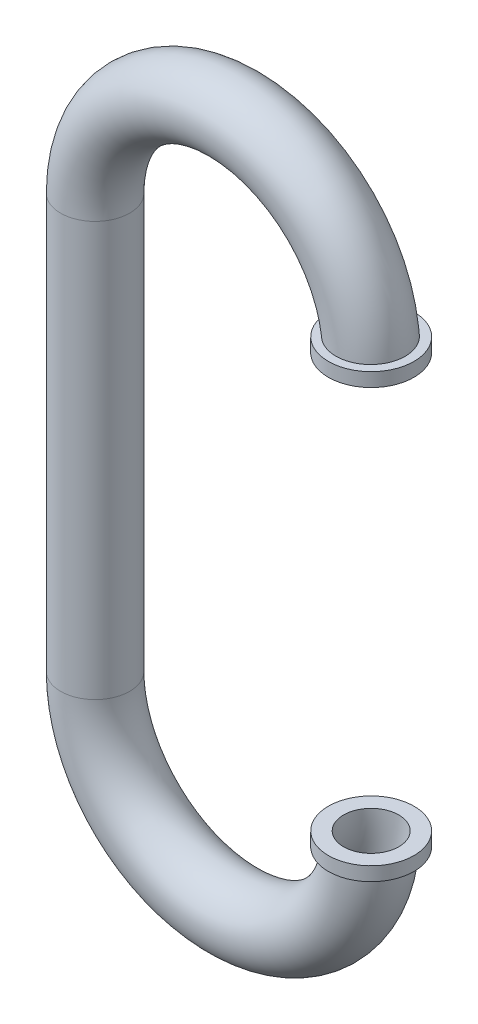
SolidWorks part; units mm, degrees
ref_plane "Ön Düzlem" through (0, 0, 0) normal (0, 0, 1) x (1, 0, 0)
ref_plane "Üst Düzlem" through (0, 0, 0) normal (0, 1, 0) x (1, 0, 0)
ref_plane "Sağ Düzlem" through (0, 0, 0) normal (1, 0, 0) x (0, 0, -1)
sketch "Çizim1" plane through (0, 0, 0) normal (0, 0, 1) x (1, 0, 0)
  line L0 (-2, 0) -> (-2, -3)
  arc A0 (0, 0) -> (-1, 1) centre (-1, 0) ccw
  arc A1 (-1, 1) -> (-2, 0) centre (-1, 0) ccw
  arc A2 (-2, -3) -> (-1, -4) centre (-1, -3) ccw
  arc A3 (-1, -4) -> (0, -3) centre (-1, -3) ccw
sketch "Çizim2" plane through (0, 0, 0) normal (0, 0, 1) x (1, 0, 0)
  line L0 (0, 0) -> (0, 0.1)
sketch "Çizim3" plane through (0, 0, 0) normal (0, 0, 1) x (1, 0, 0)
  line L0 (0, -3) -> (0, -3.1)
ref_plane "Düzlem1" through (0, -3, 0) normal (0, 1, 0) x (1, 0, 0)
sketch "Çizim4" plane through (0, 0, 0) normal (0, 1, 0) x (1, 0, 0)
  circle A0 centre (0, 0) radius 0.2
sketch "Çizim5" plane through (0, 0, 0) normal (0, 1, 0) x (1, 0, 0)
  circle A0 centre (0, 0) radius 0.21
sketch "Çizim6" plane through (0, -3, 0) normal (0, 1, 0) x (1, 0, 0)
  circle A0 centre (0, 0) radius 0.21
sweep "Süpür-İnce1" add profiles "Çizim4" path "Çizim1" parameters "D1"=0.05
sweep "Süpür-İnce2" add profiles "Çizim5" path "Çizim2" parameters "D1"=0.1
sweep "Süpür-İnce3" add profiles "Çizim6" path "Çizim3" parameters "D1"=0.1
